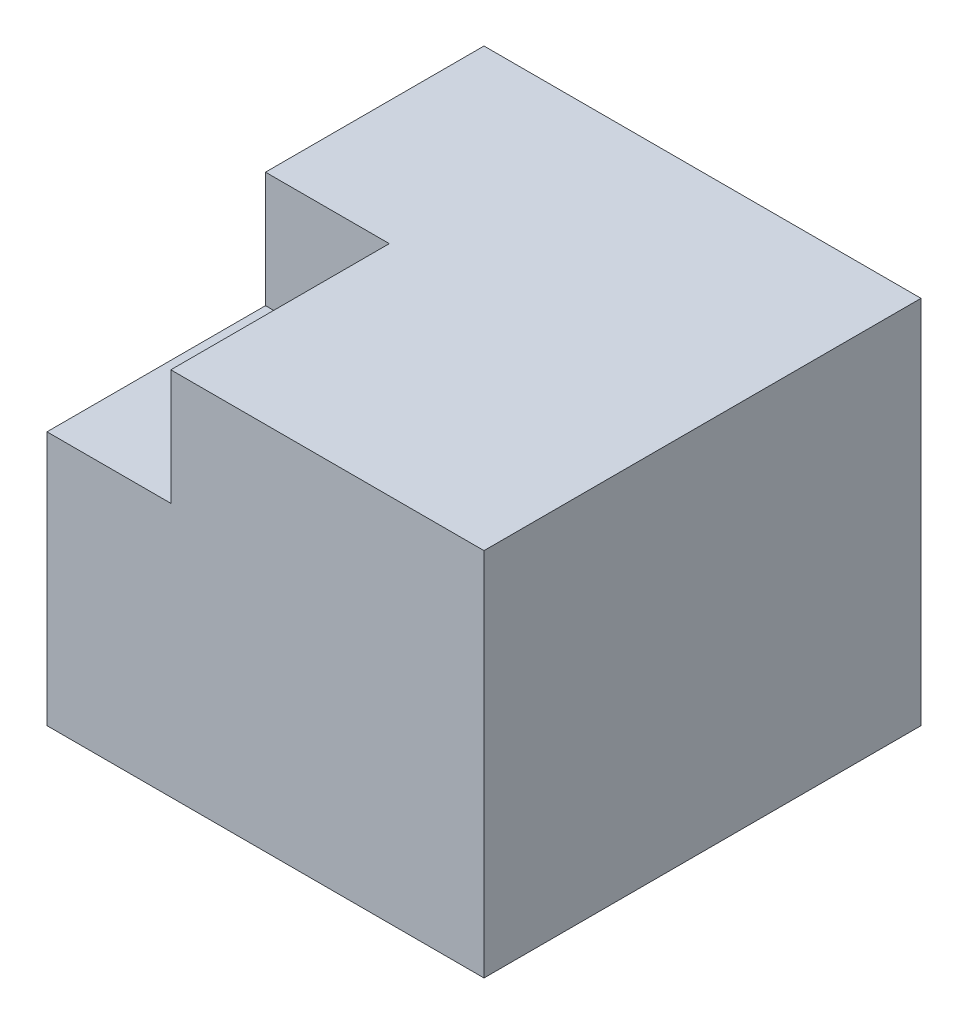
SolidWorks part; units mm, degrees
ref_plane "Front Plane" through (0, 0, 0) normal (0, 0, 1) x (1, 0, 0)
ref_plane "Top Plane" through (0, 0, 0) normal (0, 1, 0) x (1, 0, 0)
ref_plane "Right Plane" through (0, 0, 0) normal (1, 0, 0) x (0, 0, -1)
sketch "Sketch1" plane through (0, 0, 0) normal (0, 0, 1) x (1, 0, 0)
  line L1 (5, -4.2347) -> (-5, -4.2347)
  line L2 (5, -4.2347) -> (5, 4.2347)
  line L3 (5, 4.2347) -> (-5, 4.2347)
  line L4 (-5, -4.2347) -> (-5, 4.2347)
  line L5 (5, -4.2347) -> (-5, 4.2347) construction
  line L6 (5, 4.2347) -> (-5, -4.2347) construction
  point P0 (0, 0)
  dimension "D1" = 10
extrude "Boss-Extrude1" add sketch "Sketch1" along normal blind 10
sketch "Sketch2" plane through (0, 0, 10) normal (0, 0, 1) x (1, 0, 0)
  line L1 (-5, 4.2347) -> (-2.1667, 4.2347)
  line L2 (-5, 4.2347) -> (-5, 1.5893)
  line L3 (-5, 1.5893) -> (-2.1667, 1.5893)
  line L4 (-2.1667, 4.2347) -> (-2.1667, 1.5893)
extrude "Cut-Extrude1" cut sketch "Sketch2" against normal blind 5
